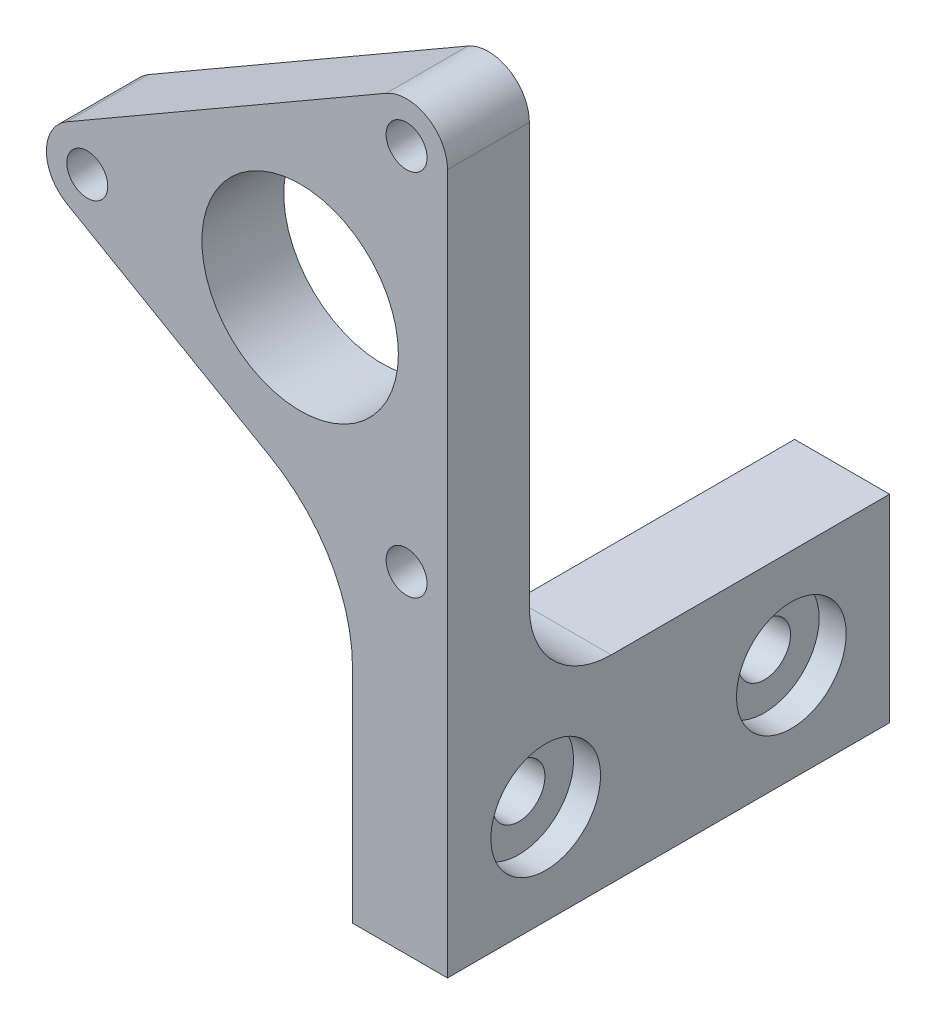
SolidWorks part; units mm, degrees
ref_plane "Plano frontal" through (0, 0, 0) normal (0, 0, 1) x (1, 0, 0)
ref_plane "Plano superior" through (0, 0, 0) normal (0, 1, 0) x (1, 0, 0)
ref_plane "Plano direito" through (0, 0, 0) normal (1, 0, 0) x (0, 0, -1)
sketch "Esboço1" plane through (0, 0, 0) normal (0, 0, 1) x (1, 0, 0)
  line L0 (0, 0) -> (-13, 0) construction
  line L1 (0, 0) -> (6.5, 11.2583) construction
  line L2 (0, 0) -> (6.5, -11.2583) construction
  line L3 (-14.25, 2.1651) -> (5.25, 13.4234)
  line L4 (-14.25, -2.1651) -> (5.25, -13.4234) construction
  line L5 (9, 11.2583) -> (9, -11.2583)
  line L6 (6.5, -11.2583) -> (6.5, -19.4083) construction
  line L7 (6.5, -19.4083) -> (3.2, -19.4083) construction
  line L8 (3.2, -19.4083) -> (3.2, -31.4983) construction
  line L9 (9, -11.2583) -> (9, -31.4983)
  line L10 (9, -31.4983) -> (3.2, -31.4983)
  line L11 (3.2, -31.4983) -> (3.2, -19.4083)
  line L12 (3.2, -19.4083) -> (3.2, -18.0133)
  line L13 (-14.25, -2.1651) -> (-1.8, -9.3531)
  circle A0 centre (0, 0) radius 6
  circle A1 centre (-13, 0) radius 2.5 construction
  circle A2 centre (6.5, -11.2583) radius 2.5 construction
  circle A3 centre (6.5, -11.2583) radius 1.25
  circle A4 centre (6.5, 11.2583) radius 2.5 construction
  circle A5 centre (6.5, 11.2583) radius 1.25
  circle A6 centre (-13, 0) radius 1.25
  arc A7 (-14.25, 2.1651) -> (-14.25, -2.1651) centre (-13, 0) ccw
  arc A8 (5.25, 13.4234) -> (9, 11.2583) centre (6.5, 11.2583) cw
  arc A9 (9, -11.2583) -> (5.25, -13.4234) centre (6.5, -11.2583) cw construction
  arc A10 (3.2, -18.0133) -> (-1.8, -9.3531) centre (-6.8, -18.0133) ccw
  point P28 (3.2, -12.2398)
  dimension "D1" = 12
  dimension "D5" = 2.5
  dimension "D6" = 5
  dimension "D10" = 10
  dimension "D2" = 120
  dimension "D3" = 120
  dimension "D4" = 13
  dimension "D7" = 8.15
  dimension "D8" = 3.3
  dimension "D9" = 12.09
extrude "Ressalto-extrusão1" add sketch "Esboço1" along normal blind 5
sketch "Esboço2" plane through (0, 0, 0) normal (0, 0, -1) x (-1, 0, 0)
  line L0 (-3.2, -31.4983) -> (-3.2, -19.4083)
  line L1 (-3.2, -18.0133) -> (-3.2, -31.4983) construction
  line L2 (-3.2, -19.4083) -> (-9, -19.4083)
  line L3 (-9, -31.4983) -> (-9, 11.2583) construction
  line L4 (-9, -19.4083) -> (-9, -31.4983)
  line L5 (-9, -31.4983) -> (-3.2, -31.4983)
  dimension "D1" = 12.09
extrude "Ressalto-extrusão2" add sketch "Esboço2" along normal blind 22
sketch "Esboço3" plane through (9, 0, 0) normal (1, 0, 0) x (0, 0, -1)
  line L0 (22, -25.4533) -> (-5, -25.4533) construction
  line L1 (22, -19.4083) -> (22, -31.4983) construction
  line L2 (-5, -31.4983) -> (-5, 11.2583) construction
  circle A0 centre (1, -25.4533) radius 1.5
  circle A1 centre (16, -25.4533) radius 1.5
  point P6 (1, -25.4533)
  point P7 (16, -25.4533)
  dimension "D3" = 3
  dimension "D1" = 6
  dimension "D2" = 6
hole_wizard "Rebaixo para SBHCS M31" positions "Esboço5" profile "Esboço6" counterbore size "M3" standard "Ansi Metric" end condition up to next
sketch "Esboço5" plane through (9, 0, 0) normal (1, 0, 0) x (0, 0, -1)
  point P0 (1, -25.4533)
  point P3 (16, -25.4533)
sketch "Esboço6" plane through (9, -25.4533, -1) normal (0, 1, 0) x (0, 0, -1)
  line L0 (0, 0) -> (0, 5.8)
  line L1 (0, 5.8) -> (1.6, 5.8)
  line L3 (1.6, 5.8) -> (1.6, 1.65)
  line L4 (1.6, 1.65) -> (3.35, 1.65)
  line L5 (3.35, 1.65) -> (3.35, 0)
  line L7 (3.35, 0) -> (0, 0)
  line L11 (0, -6.35) -> (0, 107.95) construction
  dimension "Thru Hole Dia." = 3.2
  dimension "Thru Hole Depth" = 5.8
  dimension "C'Bore Dia." = 6.7
  dimension "C'Bore Depth" = 1.65
fillet "Filete1" radius 5 1 edges
